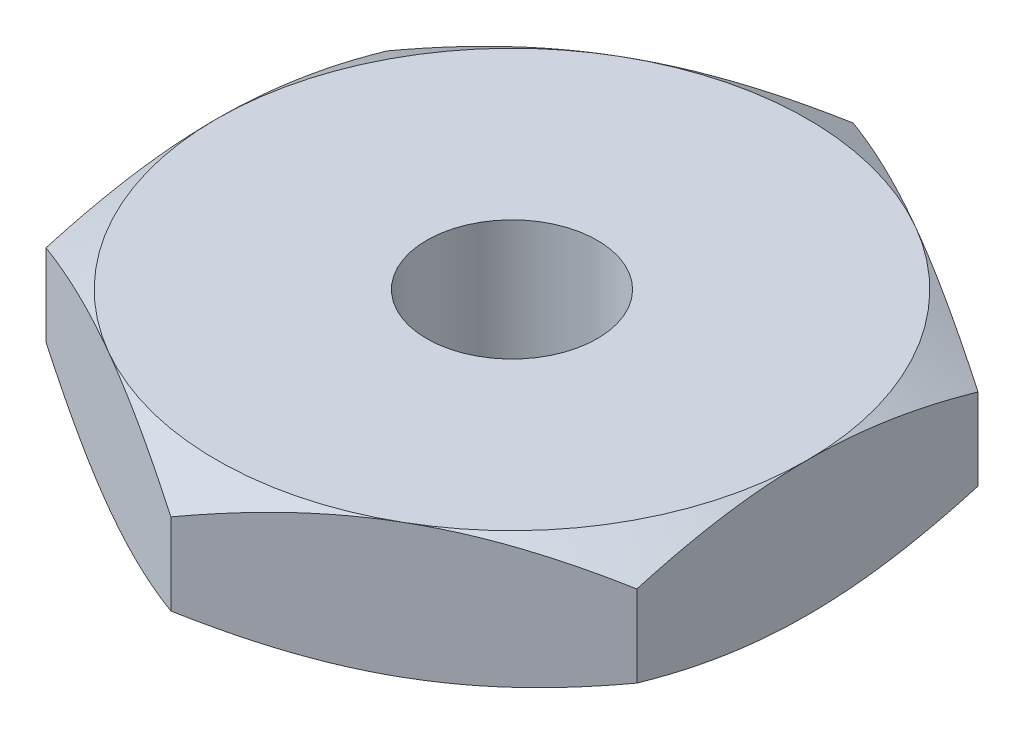
SolidWorks part; units mm, degrees
ref_plane "Front Plane" through (0, 0, 0) normal (0, 0, 1) x (1, 0, 0)
ref_plane "Top Plane" through (0, 0, 0) normal (0, 1, 0) x (1, 0, 0)
ref_plane "Right Plane" through (0, 0, 0) normal (1, 0, 0) x (0, 0, -1)
sketch "Sketch1" plane through (0, 0, 0) normal (0, 1, 0) x (1, 0, 0)
  line L1 (21.997, 12.7) -> (0, 25.4)
  line L2 (0, 25.4) -> (-21.997, 12.7)
  line L3 (-21.997, 12.7) -> (-21.997, -12.7)
  line L4 (-21.997, -12.7) -> (0, -25.4)
  line L5 (0, -25.4) -> (21.997, -12.7)
  line L6 (21.997, -12.7) -> (21.997, 12.7)
  circle A0 centre (0, 0) radius 21.997 construction
  dimension "D1" = 25.4
extrude "Boss-Extrude1" add sketch "Sketch1" along normal mid plane 10
sketch "Sketch2" plane through (0, 5, 0) normal (0, 1, 0) x (1, 0, 0)
  circle A0 centre (0, 0) radius 6.35
  dimension "D1" = 12.7
extrude "Cut-Extrude1" cut sketch "Sketch2" against normal through all
cosmetic thread "Cosmetic Thread1" parameters "D2"=14.2875
sketch "Sketch3" plane through (0, 5, 0) normal (0, 1, 0) x (1, 0, 0)
  circle A0 centre (0, 0) radius 21.997
extrude "Cut-Extrude2" cut sketch "Sketch3" against normal through all draft 60 flip side to cut
mirror "Mirror1" about plane through (0, 0, 0) normal (0, 1, 0) of "Cut-Extrude2"
